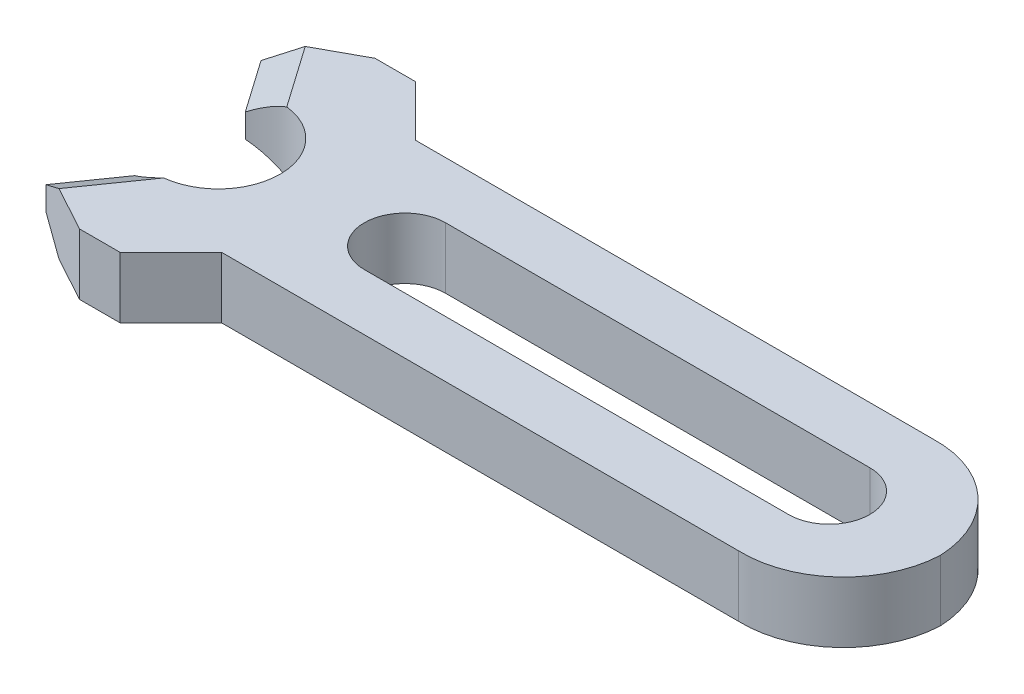
SolidWorks part; units mm, degrees
ref_plane "Front Plane" through (0, 0, 0) normal (0, 0, 1) x (1, 0, 0)
ref_plane "Top Plane" through (0, 0, 0) normal (0, 1, 0) x (1, 0, 0)
ref_plane "Right Plane" through (0, 0, 0) normal (1, 0, 0) x (0, 0, -1)
sketch "Sketch1" plane through (0, 0, 0) normal (0, 1, 0) x (1, 0, 0)
  line L3 (7.3949, 6.1456) -> (-24.9538, 6.1456)
  line L5 (17.8128, 0.0759) -> (-54.0347, 0.0759) construction
  line L9 (6.9904, 2.6159) -> (-19.5526, 2.6159)
  line L14 (6.9269, 2.6151) -> (6.9269, 2.6159)
  line L40 (-28.1288, 9.3206) -> (-30.6688, 9.3206)
  line L51 (-24.9538, 6.1456) -> (-28.1288, 9.3206)
  line L52 (-30.6688, 9.3206) -> (-35.2845, 6.8025)
  line L53 (-35.2845, 6.8025) -> (-32.9901, 3.5259)
  arc A2 (-19.5526, 2.6159) -> (-22.0926, 0.0759) centre (-19.5526, 0.0759) ccw
  arc A3 (9.5304, 0.0759) -> (6.9269, 2.6151) centre (6.9904, 0.0759) ccw
  arc A5 (13.9508, 0.0759) -> (7.3949, 6.1456) centre (7.6035, -0.2044) ccw
  arc A6 (-27.3555, 0.0759) -> (-32.9901, 3.5259) centre (-31.229, 0.0759) ccw
  point P0 (0, 0)
  point P10 (-6.6985, 0)
  dimension "D1" = 55
  dimension "D2" = 4
extrude "Boss-Extrude1" add sketch "Sketch1" along normal blind 3.8227
chamfer "Chamfer1" distance 1.17 angle 60 2 edges at (-34.1373, 0, -5.1642) (-34.1373, 3.8227, -5.1642)
mirror "Mirror1" about plane through (0, 3.8227, -0.0759) normal (0, 0, 1) of bodies 101
